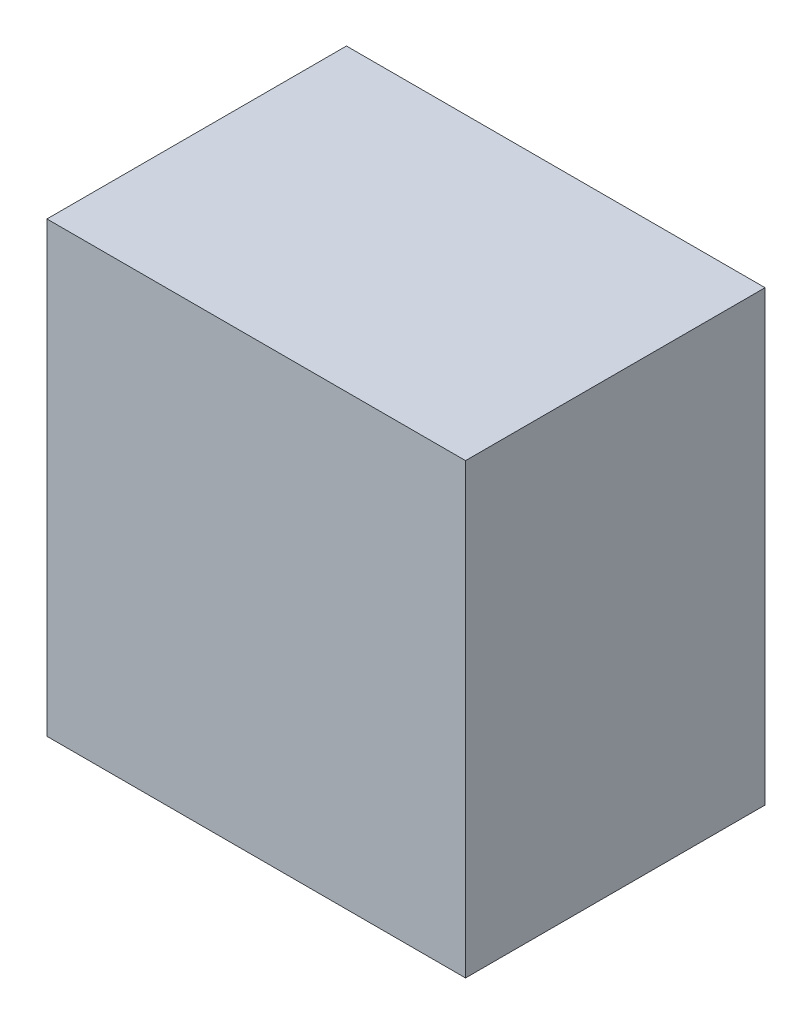
SolidWorks part; units mm, degrees
material "Balsa"
ref_plane "Front Plane" through (0, 0, 0) normal (0, 0, 1) x (1, 0, 0)
ref_plane "Top Plane" through (0, 0, 0) normal (0, 1, 0) x (1, 0, 0)
ref_plane "Right Plane" through (0, 0, 0) normal (1, 0, 0) x (0, 0, -1)
sketch "Sketch1" plane through (0, 0, 0) normal (0, 1, 0) x (1, 0, 0)
  line L1 (-35.0012, -25.0444) -> (35.0012, -25.0444)
  line L2 (-35.0012, -25.0444) -> (-35.0012, 25.0444)
  line L3 (-35.0012, 25.0444) -> (35.0012, 25.0444)
  line L4 (35.0012, -25.0444) -> (35.0012, 25.0444)
  line L5 (-35.0012, -25.0444) -> (35.0012, 25.0444) construction
  line L6 (-35.0012, 25.0444) -> (35.0012, -25.0444) construction
  point P0 (0, 0)
  dimension "D1" = 70.0024
  dimension "D2" = 50.0888
extrude "Boss-Extrude1" add sketch "Sketch1" along normal blind 74.93
